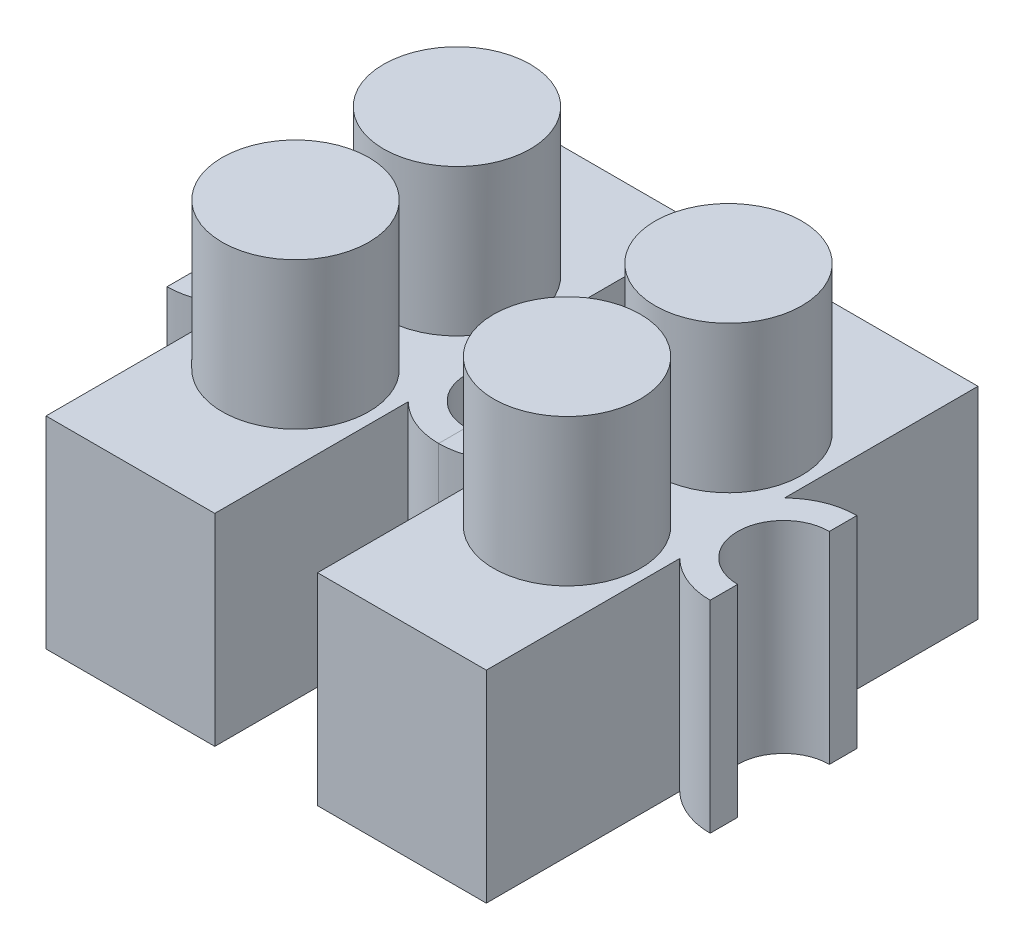
SolidWorks part; units mm, degrees
ref_plane "Front Plane" through (0, 0, 0) normal (0, 0, 1) x (1, 0, 0)
ref_plane "Top Plane" through (0, 0, 0) normal (0, 1, 0) x (1, 0, 0)
ref_plane "Right Plane" through (0, 0, 0) normal (1, 0, 0) x (0, 0, -1)
sketch "Sketch2" plane through (0, 0, 0) normal (0, 1, 0) x (1, 0, 0)
  line L0 (2.921, 8.509) -> (-2.921, 8.509)
  line L1 (-2.921, 8.509) -> (-2.921, 1.8139)
  line L2 (0, -9.3599) -> (0, 9.3599) construction
  line L3 (2.921, 8.509) -> (2.921, 1.8139)
  line L4 (-5.1689, 0) -> (5.1689, 0) construction
  line L5 (-2.921, -8.509) -> (-2.921, -1.8139)
  line L6 (2.921, -8.509) -> (2.921, -1.8139)
  line L7 (2.921, -8.509) -> (-2.921, -8.509)
  line L8 (-4.699, 2.54) -> (-4.699, -2.54) construction
  line L9 (4.699, 2.54) -> (4.699, -2.54) construction
  line L10 (-4.699, 1.5875) -> (-4.699, 2.54)
  line L11 (-4.699, -2.54) -> (-4.699, -1.5875)
  line L12 (4.699, -2.54) -> (4.699, -1.5875)
  line L13 (4.699, 1.5875) -> (4.699, 2.54)
  arc A0 (-4.699, -2.54) -> (-2.921, -1.8139) centre (-4.699, 0) ccw
  arc A1 (-4.699, 2.54) -> (-2.921, 1.8139) centre (-4.699, 0) cw
  arc A2 (4.699, -2.54) -> (2.921, -1.8139) centre (4.699, 0) cw
  arc A3 (4.699, 2.54) -> (2.921, 1.8139) centre (4.699, 0) ccw
  arc A4 (-4.699, 1.5875) -> (-4.699, -1.5875) centre (-4.699, 0) cw
  arc A5 (4.699, 1.5875) -> (4.699, -1.5875) centre (4.699, 0) ccw
  point P7 (0, 8.509)
  point P17 (-4.699, 0)
  point P18 (4.699, 0)
  dimension "D1" = 1.5875
  dimension "D2" = 5.842
  dimension "D3" = 1.778
  dimension "D4" = 5.08
  dimension "D5" = 17.018
extrude "Boss-Extrude1" add sketch "Sketch2" along normal blind 6.985 contours L3 A3 L13 A5 L12 A2 L6 L7 L5 A0 L11 A4 L10 A1 L1 L0
sketch "Sketch3" plane through (0, 0, 0) normal (0, -1, 0) x (1, 0, 0)
  line L1 (-2.286, 7.747) -> (2.286, 7.747)
  line L2 (-2.286, 7.747) -> (-2.286, -7.747)
  line L3 (-2.286, -7.747) -> (2.286, -7.747)
  line L4 (2.286, 7.747) -> (2.286, -7.747)
  line L5 (0, -7.747) -> (0, 7.747) construction
  point P4 (0, 7.747)
  point P6 (2.286, 0)
  point P7 (-2.286, 0)
  point P8 (0, -7.747)
  point P9 (0, 0)
  dimension "D1" = 4.572
  dimension "D2" = 15.494
extrude "Cut-Extrude1" cut sketch "Sketch3" against normal blind 1.27
sketch "Sketch6" plane through (0, 6.985, 0) normal (0, 1, 0) x (1, 0, 0)
  line L0 (0, -3.8418) -> (0, 3.8418) construction
  line L1 (0, 2.794) -> (0, -2.794) construction
  line L2 (-3.8418, 0) -> (3.8418, 0) construction
  line L3 (0, -5.334) -> (0, 5.334) construction
  circle A0 centre (0, 2.794) radius 2.54
  circle A1 centre (0, -2.794) radius 2.54
  point P6 (0, 0)
  dimension "D1" = 5.08
  dimension "D2" = 10.668
extrude "Boss-Extrude3" add sketch "Sketch6" along normal blind 5.08
pattern_linear "LPattern1" count 2 spacing 9.398 along (-1, 0, 0) of bodies 104
equation "\"Terminals\"= 4"
